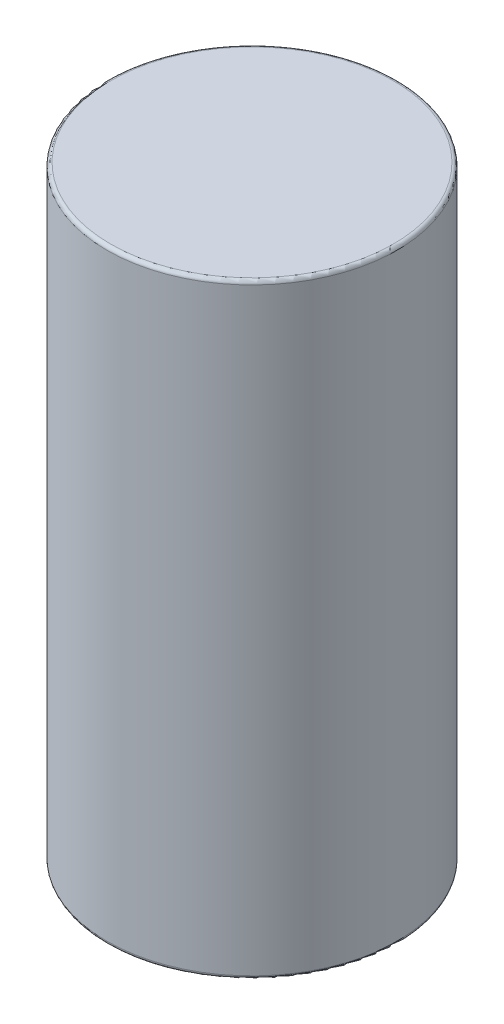
SolidWorks part; units mm, degrees
ref_plane "Спереди" through (0, 0, 0) normal (0, 0, 1) x (1, 0, 0)
ref_plane "Сверху" through (0, 0, 0) normal (0, 1, 0) x (1, 0, 0)
ref_plane "Справа" through (0, 0, 0) normal (1, 0, 0) x (0, 0, -1)
sketch "Эскиз1" plane through (0, 0, 0) normal (0, 1, 0) x (1, 0, 0)
  circle A0 centre (0, 0) radius 4
  dimension "D1" = 8
extrude "Бобышка-Вытянуть1" add sketch "Эскиз1" along normal blind 16.7
fillet "Скругление1" radius 0.1 1 edges at (0, 16.7, 4)
fillet "Скругление2" radius 0.1 1 edges at (0, 0, 4)
